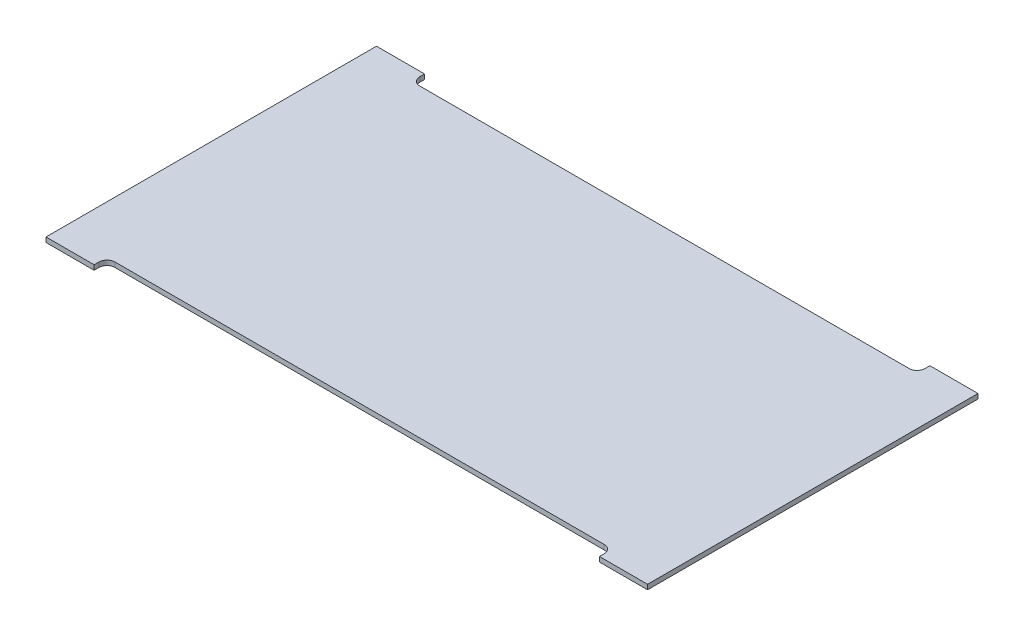
SolidWorks part; units mm, degrees
ref_plane "Front Plane" through (0, 0, 0) normal (0, 0, 1) x (1, 0, 0)
ref_plane "Top Plane" through (0, 0, 0) normal (0, 1, 0) x (1, 0, 0)
ref_plane "Right Plane" through (0, 0, 0) normal (1, 0, 0) x (0, 0, -1)
sketch "Sketch1" plane through (0, 0, 0) normal (0, 1, 0) x (1, 0, 0)
  line L0 (0, 190) -> (-750, 190) construction
  line L1 (0, 0) -> (-690, 0) construction
  line L2 (0, 0) -> (0, 380) construction
  line L3 (0, 380) -> (-750, 380) construction
  line L4 (-750, -16) -> (-750, 380) construction
  line L5 (-375, 380) -> (-375, 0) construction
  line L6 (-750, 396) -> (-690, 396)
  line L7 (-750, -16) -> (-690, -16)
  line L8 (-690, 0) -> (-690, -16)
  line L9 (-690, 380) -> (-690, 396)
  line L10 (-60, 0) -> (-60, -16)
  line L11 (0, -16) -> (-60, -16)
  line L12 (-60, 380) -> (-60, 396)
  line L13 (0, 396) -> (-60, 396)
  line L14 (0, 396) -> (0, -16)
  line L15 (-60, 380) -> (-690, 380)
  line L16 (-750, 396) -> (-750, -16)
  line L17 (-60, 0) -> (-690, 0)
  dimension "D1" = 750
  dimension "D4" = 60
  dimension "D2" = 380
  dimension "D3" = 16
extrude "Boss-Extrude1" add sketch "Sketch1" along normal blind 6
fillet "Fillet1" radius 10 4 edges at (-60, 3, -380) (-690, 3, -380) (-690, 3, 0) (-60, 3, 0)
equation "\"D1@Sketch1\"=1.5*500"
